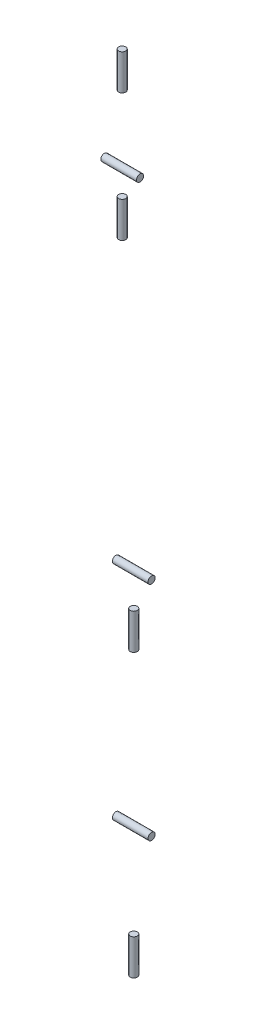
SolidWorks part; units mm, degrees
ref_plane "Front Plane" through (0, 0, 0) normal (0, 0, 1) x (1, 0, 0)
ref_plane "Top Plane" through (0, 0, 0) normal (0, 1, 0) x (1, 0, 0)
ref_plane "Right Plane" through (0, 0, 0) normal (1, 0, 0) x (0, 0, -1)
sketch "Sketch1" plane through (0, 0, 0) normal (0, 1, 0) x (1, 0, 0)
  circle A0 centre (0, 0) radius 2.5
  dimension "D1" = 5
extrude "Axis 0 - AX12" add sketch "Sketch1" along normal blind 25
ref_plane "Plane1" through (0, 90.525, 0) normal (0, 1, 0) x (-1, 0, 0)
sketch "Sketch2" plane through (0, 0, 0) normal (1, 0, 0) x (0, 0, -1)
  line L0 (114.018, 90.525) -> (-114.018, 90.525) construction
  circle A0 centre (0, 90.525) radius 2.5
  dimension "D1" = 5
extrude "Axis 1 - EX106" add sketch "Sketch2" along normal mid plane 25 separate body
ref_plane "Plane3" through (0, 210.225, 0) normal (0, 1, 0) x (-1, 0, 0)
sketch "Sketch3" plane through (0, 210.225, 0) normal (0, 1, 0) x (-1, 0, 0)
  circle A0 centre (0, 0) radius 2.5
  dimension "D1" = 5
extrude "Axis 2 - RX64 1" add sketch "Sketch3" along normal mid plane 25 separate body
ref_plane "Plane4" through (0, 246.225, 0) normal (0, 1, 0) x (-1, 0, 0)
sketch "Sketch4" plane through (0, 0, 0) normal (1, 0, 0) x (0, 0, -1)
  line L0 (114.018, 246.225) -> (-114.018, 246.225) construction
  line L2 (0, 24.6962) -> (0, -24.6962) construction
  circle A0 centre (0, 246.225) radius 2.5
  dimension "D1" = 5
extrude "Axis 3 - RX64 2" add sketch "Sketch4" along normal mid plane 25 separate body
ref_plane "Plane5" through (0, 0, 8.1) normal (0, 0, 1) x (1, 0, 0)
ref_plane "Plane6" through (0, 464.425, 0) normal (0, 1, 0) x (-1, 0, 0)
sketch "Sketch5" plane through (0, 464.425, 0) normal (0, 1, 0) x (-1, 0, 0)
  line L0 (21.2453, 8.1) -> (-21.2453, 8.1) construction
  circle A0 centre (0, 8.1) radius 2.5
  dimension "D1" = 5
extrude "Axis 4 - RX28 1" add sketch "Sketch5" along normal mid plane 25 separate body
ref_plane "Plane7" through (0, 494.425, 0) normal (0, 1, 0) x (-1, 0, 0)
sketch "Sketch6" plane through (0, 0, 0) normal (1, 0, 0) x (0, 0, -1)
  line L0 (-8.1, 21.2453) -> (-8.1, -21.2453) construction
  line L1 (114.018, 494.425) -> (-114.018, 494.425) construction
  circle A0 centre (-8.1, 494.425) radius 2.5
  dimension "D1" = 5
extrude "Axis 5 - RX28 2" add sketch "Sketch6" along normal mid plane 25 separate body
ref_plane "Plane8" through (0, 554.025, 0) normal (0, 1, 0) x (-1, 0, 0)
sketch "Sketch7" plane through (0, 554.025, 0) normal (0, 1, 0) x (-1, 0, 0)
  line L0 (21.2453, 8.1) -> (-21.2453, 8.1) construction
  circle A0 centre (0, 8.1) radius 2.5
  dimension "D1" = 5
extrude "Boss-Extrude1" add sketch "Sketch7" along normal mid plane 25 separate body
equation "\"D1@Sketch2\" = \"D1@Sketch1\""
equation "\"D1@Sketch3\" = \"D1@Sketch2\""
equation "\"D1@Axis 1 - EX106\" = \"D1@Axis 0 - AX12\""
equation "\"D1@Axis 2 - RX64 1\" = \"D1@Axis 1 - EX106\""
equation "\"D1@Sketch4\" = \"D1@Sketch3\""
equation "\"D1@Axis 3 - RX64 2\" = \"D1@Axis 2 - RX64 1\""
equation "\"D1@Sketch5\" = \"D1@Sketch4\""
equation "\"D1@Axis 4 - RX28 1\" = \"D1@Axis 3 - RX64 2\""
equation "\"D1@Sketch6\" = \"D1@Sketch5\""
equation "\"D1@Axis 5 - RX28 2\" = \"D1@Axis 4 - RX28 1\""
equation "\"D1@Sketch7\" = \"D1@Sketch6\""
equation "\"D1@Boss-Extrude1\" = \"D1@Axis 5 - RX28 2\""
